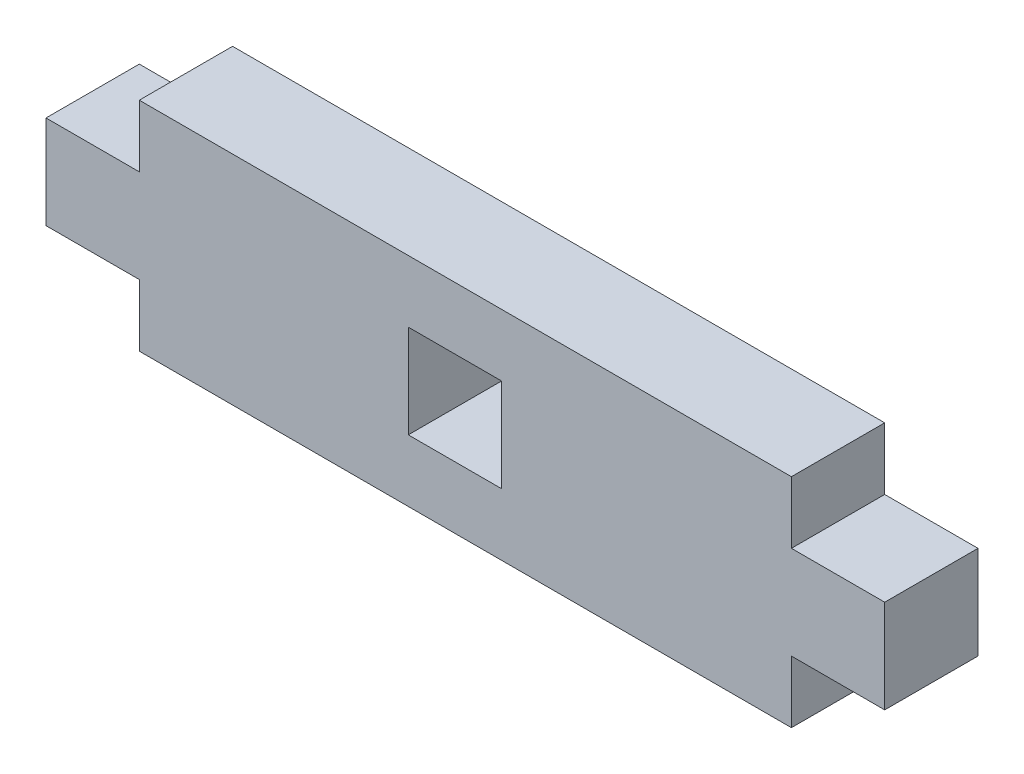
SolidWorks part; units mm, degrees
ref_plane "Front Plane" through (0, 0, 0) normal (0, 0, 1) x (1, 0, 0)
ref_plane "Top Plane" through (0, 0, 0) normal (0, 1, 0) x (1, 0, 0)
ref_plane "Right Plane" through (0, 0, 0) normal (1, 0, 0) x (0, 0, -1)
sketch "Sketch2" plane through (0, 0, 0) normal (0, 0, 1) x (1, 0, 0)
  line L0 (0, 3.425) -> (0, 8.575)
  line L1 (0, -55) -> (0, 55) construction
  line L2 (0, 8.575) -> (5.15, 8.575)
  line L3 (5.15, 8.575) -> (5.15, 12)
  line L4 (55, 0) -> (-55, 0) construction
  line L5 (5.15, 0) -> (41.15, 0)
  line L6 (41.15, 8.575) -> (41.15, 12)
  line L7 (41.15, 8.575) -> (46.3, 8.575)
  line L8 (46.3, 8.575) -> (46.3, 3.425)
  line L9 (46.3, 3.425) -> (41.15, 3.425)
  line L10 (41.15, 0) -> (41.15, 3.425)
  line L11 (41.15, 12) -> (5.15, 12)
  line L12 (5.15, 0) -> (5.15, 3.425)
  line L13 (5.15, 3.425) -> (0, 3.425)
  dimension "D1" = 36
  dimension "D2" = 5.15
  dimension "D3" = 12
  dimension "D4" = 5.15
extrude "Boss-Extrude1" add sketch "Sketch2" along normal blind 5.15
sketch "Sketch3" plane through (0, 0, 5.15) normal (0, 0, 1) x (1, 0, 0)
  line L0 (41.15, 0) -> (41.15, 3.425) construction
  line L1 (41.15, 12) -> (5.15, 12) construction
  line L2 (20, 8.575) -> (20, 3.425)
  line L3 (46.3, 8.575) -> (41.15, 8.575) construction
  line L4 (25.15, 3.425) -> (20, 3.425)
  line L5 (41.15, 3.425) -> (46.3, 3.425) construction
  line L9 (25.15, 8.575) -> (25.15, 3.425)
  line L10 (25.15, 8.575) -> (20, 8.575)
  line L12 (23.15, 12) -> (23.15, -3.9207) construction
  dimension "D1" = 16
extrude "Cut-Extrude1" cut sketch "Sketch3" against normal through all
